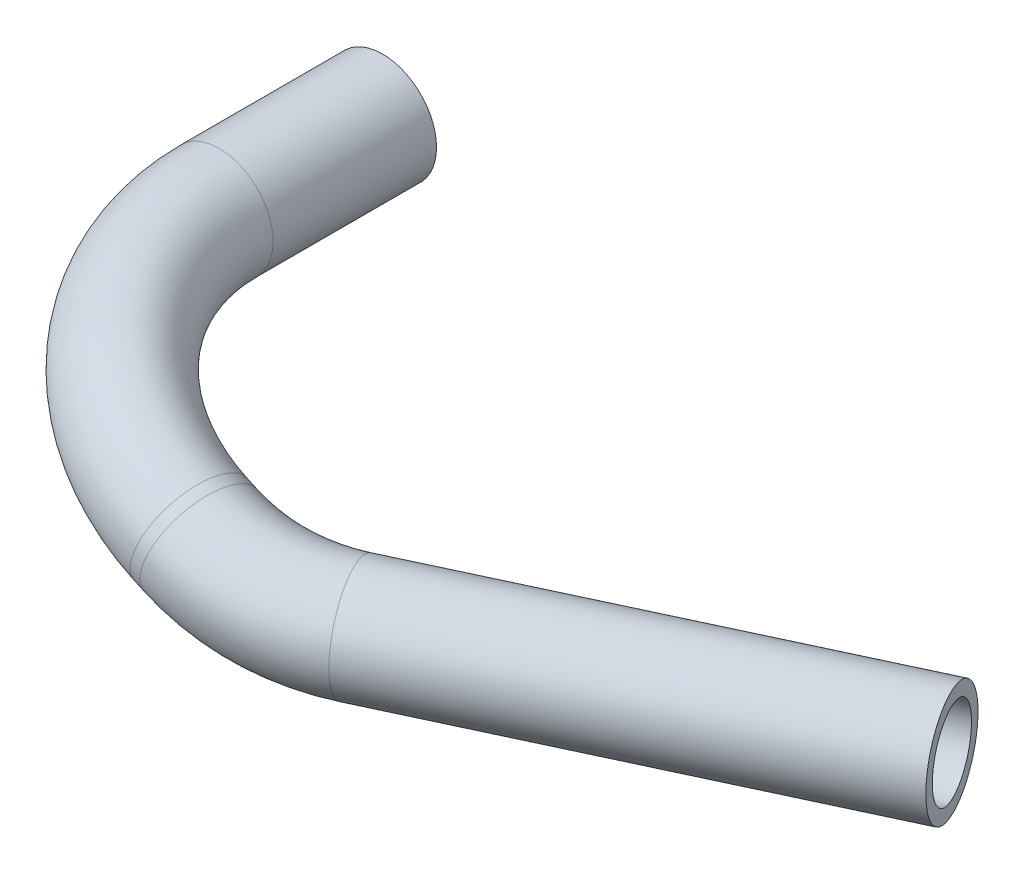
SolidWorks part; units mm, degrees
material "ПК/АБС"
ref_plane "Спереди" through (0, 0, 0) normal (0, 0, 1) x (1, 0, 0)
ref_plane "Сверху" through (0, 0, 0) normal (0, 1, 0) x (1, 0, 0)
ref_plane "Справа" through (0, 0, 0) normal (1, 0, 0) x (0, 0, -1)
sketch "Эскиз1" plane through (0, 0, 0) normal (0, 0, 1) x (1, 0, 0)
  circle A0 centre (0, 0) radius 3.58
  circle A1 centre (0, 0) radius 4.765
  dimension "D1" = 7.16
  dimension "D2" = 9.53
sketch3d "Трехмерный эскиз1"
  line L0 (0, 0, 0) -> (0, 0, 14.4605)
  line L1 (29.9144, -8, 32.3626) -> (65.9384, -8, 15.5764)
  line L2 (18.3244, -6.0467, 34.4731) -> (17.3782, -5.7345, 34.3881)
  arc A0 (17.3782, -5.7345, 34.3881) -> (0, 0, 14.4605) centre (18.9927, -6.2672, 14.4605) ccw
  arc A1 (29.9144, -8, 32.3626) -> (18.3244, -6.0467, 34.4731) centre (22.8479, 2.9583, 17.1975) ccw
  point P7 (0, 0, 32.8269)
  point P8 (12.7255, -25.2599, 14.4605)
  point P11 (24.2438, -8, 35.0049)
  point P12 (18.2195, -13.7723, 7.2646)
  dimension "D1" = 20
  dimension "D2" = 20
  dimension "D3" = 8
  dimension "D4" = 1
sweep "По траектории1" add profiles "Эскиз1" path "Трехмерный эскиз1"
